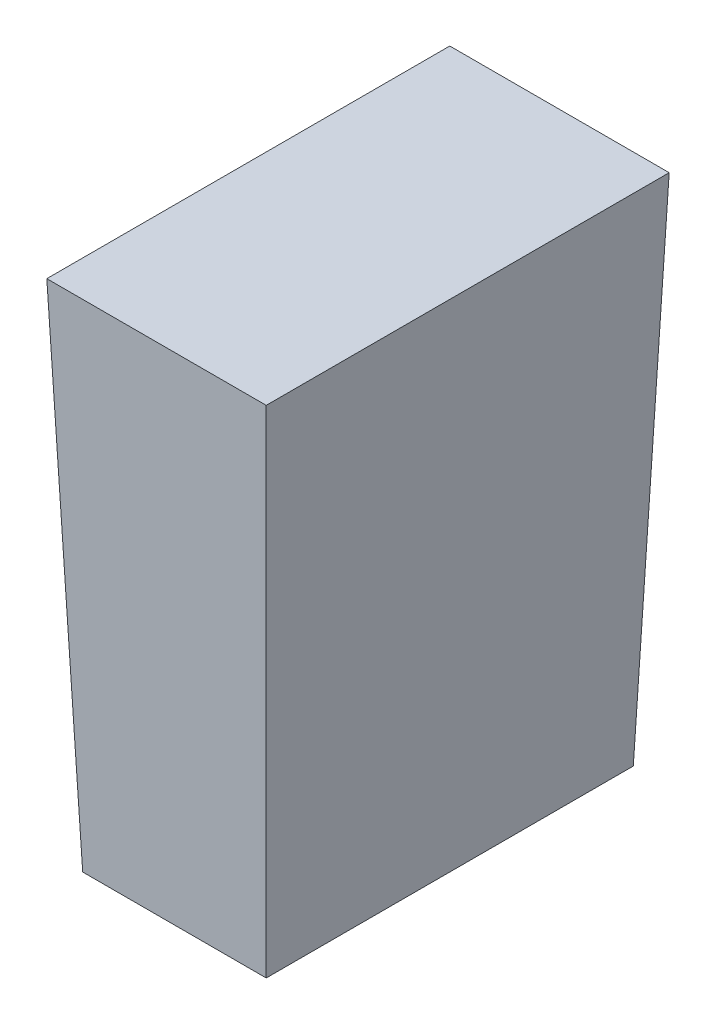
SolidWorks part; units mm, degrees
ref_plane "Front Plane" through (0, 0, 0) normal (0, 0, 1) x (1, 0, 0)
ref_plane "Top Plane" through (0, 0, 0) normal (0, 1, 0) x (1, 0, 0)
ref_plane "Right Plane" through (0, 0, 0) normal (1, 0, 0) x (0, 0, -1)
sketch "Sketch1" plane through (0, 0, 0) normal (0, 1, 0) x (1, 0, 0)
  line L1 (1.5875, 3.175) -> (-1.5875, 3.175)
  line L2 (1.5875, 3.175) -> (1.5875, -3.175)
  line L3 (1.5875, -3.175) -> (-1.5875, -3.175)
  line L4 (-1.5875, 3.175) -> (-1.5875, -3.175)
  line L5 (1.5875, 3.175) -> (-1.5875, -3.175) construction
  line L6 (1.5875, -3.175) -> (-1.5875, 3.175) construction
  point P0 (0, 0)
  dimension "D1" = 6.35
  dimension "D2" = 3.175
extrude "Boss-Extrude1" add sketch "Sketch1" along normal blind 8.89 draft 2 draft outward yes
